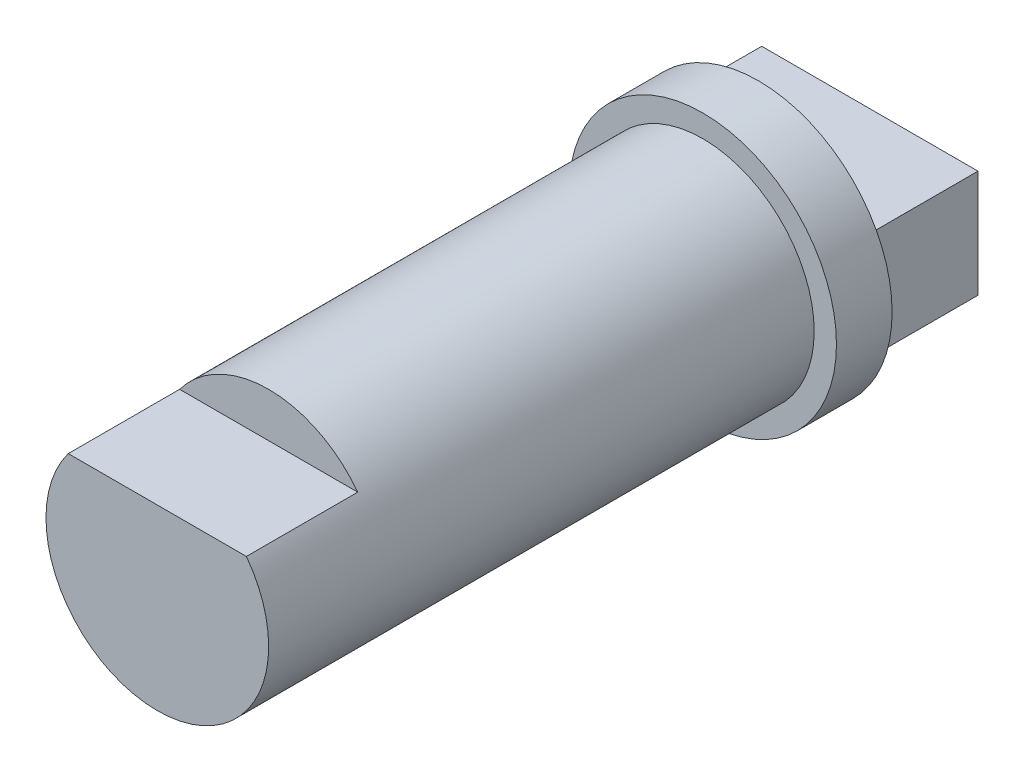
SolidWorks part; units mm, degrees
ref_plane "Front Plane" through (0, 0, 0) normal (0, 0, 1) x (1, 0, 0)
ref_plane "Top Plane" through (0, 0, 0) normal (0, 1, 0) x (1, 0, 0)
ref_plane "Right Plane" through (0, 0, 0) normal (1, 0, 0) x (0, 0, -1)
sketch "Sketch1" plane through (0, 0, 0) normal (0, 0, 1) x (1, 0, 0)
  circle A0 centre (0, 0) radius 10
extrude "Boss-Extrude1" add sketch "Sketch1" along normal blind 49
sketch "Sketch2" plane through (0, 0, 0) normal (0, 0, -1) x (-1, 0, 0)
  circle A0 centre (0, 0) radius 12
extrude "Boss-Extrude2" add sketch "Sketch2" along normal blind 5
sketch "Sketch3" plane through (0, 0, 49) normal (0, 0, 1) x (1, 0, 0)
  line L0 (0, 0) -> (0, 6)
  line L1 (8, 6) -> (-8, 6)
  circle A0 centre (0, 0) radius 10
  point P7 (0, 6)
  circle M3 centre (0, 0) radius 10
extrude "Cut-Extrude1" cut sketch "Sketch3" against normal blind 10 contours L1 M3
sketch "Sketch4" plane through (0, 0, -5) normal (0, 0, -1) x (-1, 0, 0)
  line L1 (-9.7143, 4.8277) -> (9.7143, 4.8277)
  line L2 (-9.7143, 4.8277) -> (-9.7143, -4.8277)
  line L3 (-9.7143, -4.8277) -> (9.7143, -4.8277)
  line L4 (9.7143, 4.8277) -> (9.7143, -4.8277)
  line L5 (-9.7143, 4.8277) -> (9.7143, -4.8277) construction
  line L6 (-9.7143, -4.8277) -> (9.7143, 4.8277) construction
  point P0 (0, 0)
extrude "Boss-Extrude3" add sketch "Sketch4" along normal blind 10
